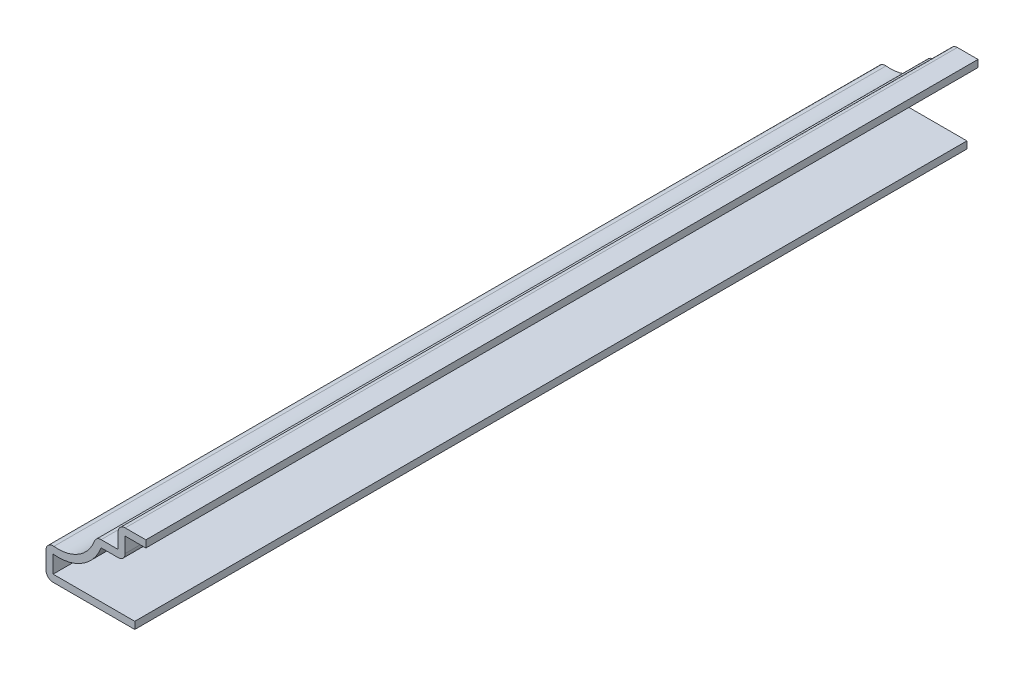
SolidWorks part; units mm, degrees
ref_plane "Front Plane" through (0, 0, 0) normal (0, 0, 1) x (1, 0, 0)
ref_plane "Top Plane" through (0, 0, 0) normal (0, 1, 0) x (1, 0, 0)
ref_plane "Right Plane" through (0, 0, 0) normal (1, 0, 0) x (0, 0, -1)
sketch "Sketch1" plane through (0, 0, 0) normal (0, 0, 1) x (1, 0, 0)
  line L0 (0, 0) -> (-12.7, 0)
  line L1 (-12.7, 0) -> (-12.7, 4.7625)
  line L4 (-5.5562, 8.7312) -> (-2.3812, 8.7312)
  line L5 (-2.3812, 8.7312) -> (-2.3812, 11.9062)
  line L6 (-2.3812, 11.9062) -> (1.5875, 11.9062)
  arc A0 (-12.7, 4.7625) -> (-5.5562, 8.7312) centre (-10.9566, 10.0382) ccw
  point P5 (-5.5563, 7.2361)
  point P10 (-5.5563, 7.1596)
  dimension "D6" = 5.5562
  dimension "D1" = 12.7
  dimension "D2" = 14.2875
  dimension "D3" = 3.9688
  dimension "D4" = 3.175
  dimension "D5" = 4.7625
  dimension "D7" = 3.175
  dimension "D8" = 11.9062
extrude "Extrude-Thin1" add sketch "Sketch1" against normal blind 119.0625 thin
fillet "Fillet1" radius 1.016 5 edges at (-1.3652, 7.7153, -59.5312) (-2.3812, 11.9062, -59.5312) (-5.5563, 8.7312, -59.5312) (-12.7, 4.7625, -59.5312) (-12.7, 0, -59.5312)
